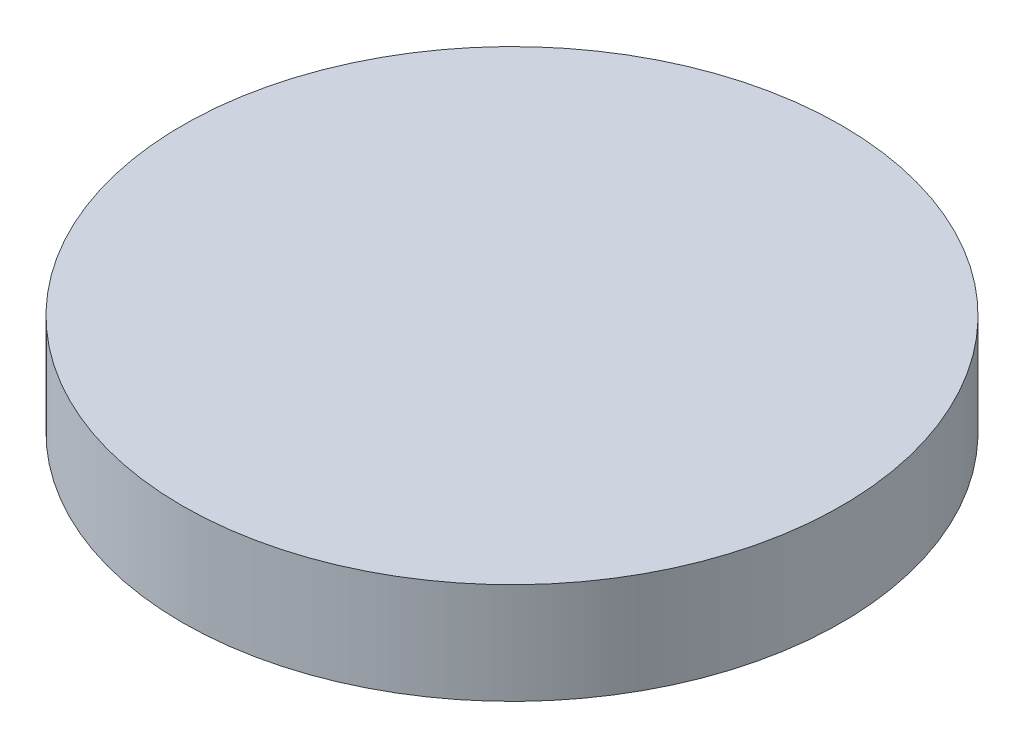
SolidWorks part; units mm, degrees
ref_plane "Front Plane" through (0, 0, 0) normal (0, 0, 1) x (1, 0, 0)
ref_plane "Top Plane" through (0, 0, 0) normal (0, 1, 0) x (1, 0, 0)
ref_plane "Right Plane" through (0, 0, 0) normal (1, 0, 0) x (0, 0, -1)
sketch "Sketch1" plane through (0, 0, 0) normal (0, 1, 0) x (1, 0, 0)
  circle A0 centre (0, 0) radius 3.2606
  dimension "D1" = 6.5211
extrude "Boss-Extrude1" add sketch "Sketch1" along normal blind 1
